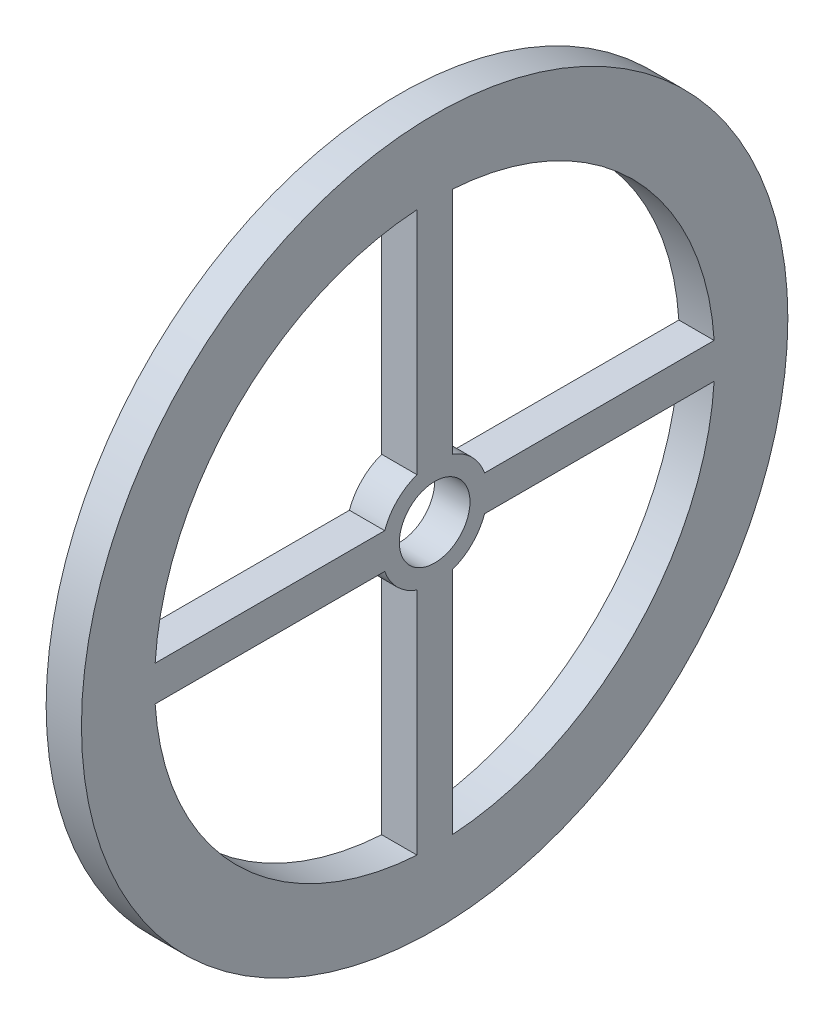
SolidWorks part; units mm, degrees
ref_plane "Front Plane" through (0, 0, 0) normal (0, 0, 1) x (1, 0, 0)
ref_plane "Top Plane" through (0, 0, 0) normal (0, 1, 0) x (1, 0, 0)
ref_plane "Right Plane" through (0, 0, 0) normal (1, 0, 0) x (0, 0, -1)
sketch "Sketch1" plane through (0, 0, 0) normal (1, 0, 0) x (0, 0, -1)
  line L2 (-5, 79.1287) -> (-5, 14.1421)
  line L4 (5, 79.1287) -> (5, 14.1421)
  line L5 (14.1421, 5) -> (79.1287, 5)
  line L7 (14.1421, -5) -> (79.1287, -5)
  line L10 (-5, -14.1421) -> (-5, -79.1287)
  line L12 (5, -14.1421) -> (5, -79.1287)
  line L17 (-79.1287, -5) -> (-14.1421, -5)
  line L19 (-79.1287, 5) -> (-14.1421, 5)
  circle A0 centre (0, 0) radius 100
  circle A1 centre (0, 0) radius 79.2865
  circle A2 centre (0, 0) radius 10
  circle A3 centre (0, 0) radius 15
  dimension "D1" = 200
  dimension "D2" = 20
  dimension "D3" = 30
  dimension "D4" = 10
  dimension "D5" = 10
  dimension "D6" = 10
  dimension "D7" = 10
extrude "Boss-Extrude1" add sketch "Sketch1" along normal blind 10 contours A0 A1 | A3 L10 A1 L12 | A3 L19 A1 L17 | A3 L4 A1 L2 | A3 L7 A1 L5 | A3 A2
